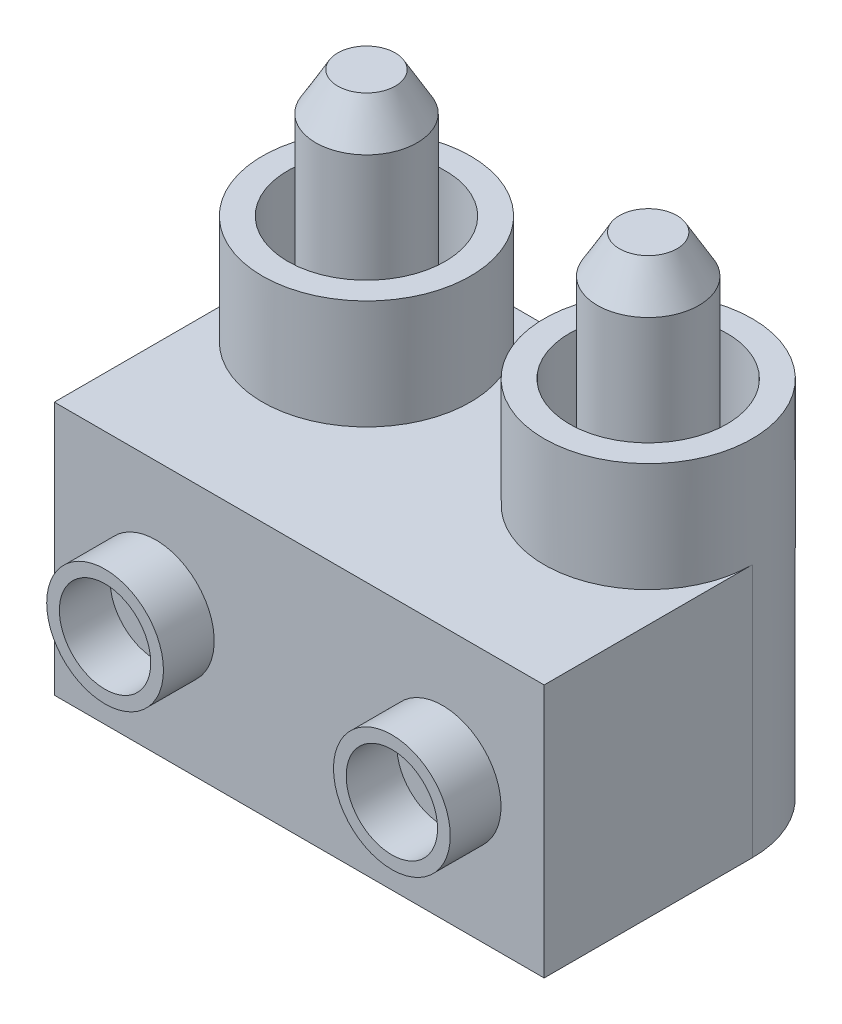
SolidWorks part; units mm, degrees
ref_plane "Front Plane" through (0, 0, 0) normal (0, 0, 1) x (1, 0, 0)
ref_plane "Top Plane" through (0, 0, 0) normal (0, 1, 0) x (1, 0, 0)
ref_plane "Right Plane" through (0, 0, 0) normal (1, 0, 0) x (0, 0, -1)
sketch "Sketch2" plane through (0, 0, 0) normal (0, 1, 0) x (1, 0, 0)
  line L1 (-5.55, 6.15) -> (5.55, 6.15)
  line L2 (-9.65, 2.05) -> (-9.65, -6.15)
  line L3 (-9.65, -6.15) -> (9.65, -6.15)
  line L4 (9.65, 2.05) -> (9.65, -6.15)
  arc A0 (9.65, 2.05) -> (5.55, 6.15) centre (5.55, 2.05) ccw
  arc A1 (-5.55, 6.15) -> (-9.65, 2.05) centre (-5.55, 2.05) ccw
  dimension "D5" = 4.1
  dimension "D1" = 19.3
  dimension "D2" = 12.3
  dimension "D3" = 6.15
  dimension "D4" = 9.65
extrude "Boss-Extrude1" add sketch "Sketch2" along normal blind 10
sketch "Sketch3" plane through (0, 10, 0) normal (0, 1, 0) x (1, 0, 0)
  line L0 (-9.65, 2.05) -> (-5.55, 2.05) construction
  line L1 (9.65, 2.05) -> (5.55, 2.05) construction
  arc A0 (9.65, 2.05) -> (5.55, 6.15) centre (5.55, 2.05) ccw construction
  circle A1 centre (-5.55, 2.05) radius 4.1
  circle A2 centre (5.55, 2.05) radius 4.1
  circle A3 centre (-5.55, 2.05) radius 3.1
  circle A4 centre (5.55, 2.05) radius 3.1
  dimension "D1" = 1
extrude "Boss-Extrude2" add sketch "Sketch3" along normal blind 4.3
sketch "Sketch4" plane through (0, 10, 0) normal (0, 1, 0) x (1, 0, 0)
  line L0 (-8.65, 2.05) -> (-2.45, 2.05) construction
  line L1 (2.45, 2.05) -> (8.65, 2.05) construction
  circle A0 centre (-5.55, 2.05) radius 3.1 construction
  circle A1 centre (-5.55, 2.05) radius 3.1 construction
  circle A2 centre (5.55, 2.05) radius 3.1 construction
  circle A3 centre (-5.55, 2.05) radius 2
  circle A4 centre (5.55, 2.05) radius 2
  dimension "D1" = 4
  dimension "D2" = 4
extrude "Boss-Extrude3" add sketch "Sketch4" along normal blind 9.3 separate body
chamfer "Chamfer1" distance 1.5 angle 30 1 edges at (-5.55, 19.3, -0.05)
chamfer "Chamfer2" distance 1.5 angle 30 1 edges at (5.55, 19.3, -0.05)
sketch "Sketch5" plane through (0, 0, 6.15) normal (0, 0, 1) x (1, 0, 0)
  line L0 (-9.65, 5) -> (9.65, 5) construction
  line L1 (-9.65, 10) -> (-9.65, 0) construction
  line L2 (9.65, 10) -> (9.65, 0) construction
  line L3 (5.65, 5) -> (5.65, 2.122) construction
  line L4 (-5.65, 5) -> (-5.65, 2.581) construction
  circle A0 centre (-5.65, 5) radius 2.3
  circle A1 centre (5.65, 5) radius 2.3
  circle A2 centre (-5.65, 5) radius 1.8
  circle A3 centre (5.65, 5) radius 1.8
  dimension "D3" = 4.6
  dimension "D4" = 4.6
  dimension "D1" = 4
  dimension "D2" = 4
  dimension "D5" = 0.5
extrude "Boss-Extrude4" add sketch "Sketch5" along normal blind 2
